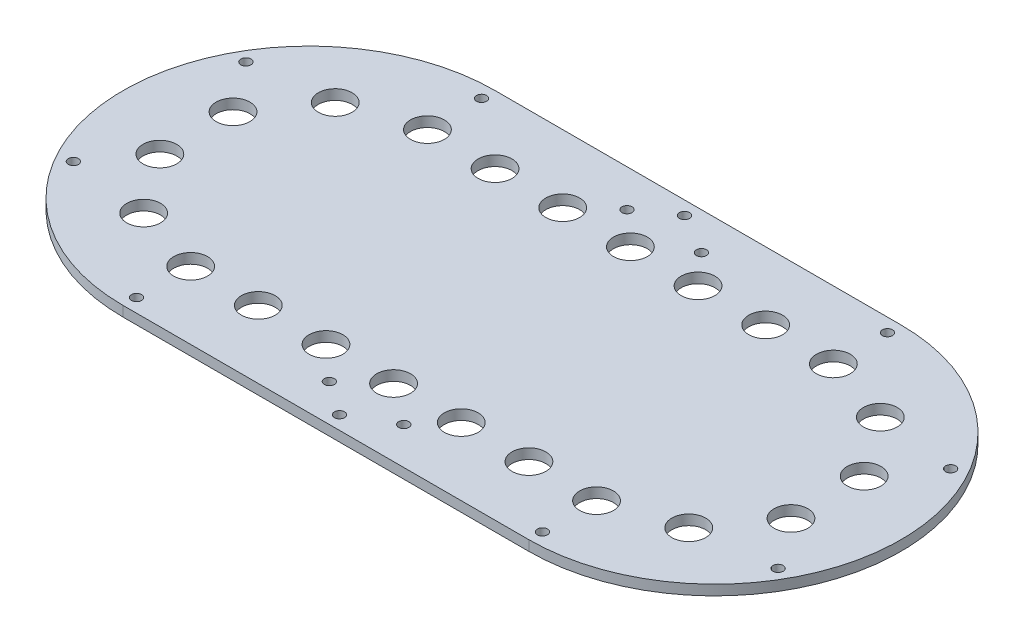
SolidWorks part; units mm, degrees
ref_plane "前视基准面" through (0, 0, 0) normal (0, 0, 1) x (1, 0, 0)
ref_plane "上视基准面" through (0, 0, 0) normal (0, 1, 0) x (1, 0, 0)
ref_plane "右视基准面" through (0, 0, 0) normal (1, 0, 0) x (0, 0, -1)
sketch "草图1" plane through (0, 0, 0) normal (0, 1, 0) x (1, 0, 0)
  line L0 (0, 0) -> (0, 89.0672) construction
  line L1 (-60, 0) -> (60, 0) construction
  line L2 (-60, 70) -> (60, 70)
  line L3 (-60, -70) -> (60, -70)
  line L4 (-90, 51.9615) -> (-60, 0) construction
  line L5 (-90, -51.9615) -> (-60, 0) construction
  line L8 (0, 0) -> (76.6344, 0) construction
  line L9 (-49.5811, 59.0885) -> (-60, 0) construction
  line L10 (-116.3816, -20.5212) -> (-60, 0) construction
  line L11 (-14.0373, -38.5673) -> (-60, 0) construction
  arc A2 (-60, 70) -> (-60, -70) centre (-60, 0) ccw
  arc A3 (60, -70) -> (60, 70) centre (60, 0) ccw
  circle A4 centre (0, 0) radius 1.5 construction
  circle A5 centre (-90, 51.9615) radius 1.5 construction
  circle A6 centre (-90, -51.9615) radius 1.5 construction
  circle A7 centre (90, -51.9615) radius 1.5 construction
  circle A8 centre (90, 51.9615) radius 1.5 construction
  circle A10 centre (-122, 0) radius 1.5
  circle A11 centre (122, 0) radius 1.5
  circle A12 centre (-30, 60) radius 1.5
  circle A13 centre (30, 60) radius 1.5
  circle A14 centre (30, -60) radius 1.5
  circle A15 centre (-30, -60) radius 1.5
  point P7 (0, 0)
  dimension "D4" = 3
  dimension "D7" = 3
  dimension "D9" = 3
  dimension "D10" = 60
  dimension "D12" = 3
  dimension "D13" = 62
  dimension "D14" = 62
  dimension "D15" = 3
  dimension "D16" = 3
  dimension "D18" = 60
  dimension "D8" = 120
  dimension "D11" = 120
  dimension "D17" = 30
  dimension "D20" = 60
  dimension "D21" = 80
  dimension "D24" = 120
  dimension "D26" = 60
  dimension "D27" = 120
extrude "凸台-拉伸2" add sketch "草图1" along normal blind 3
sketch "草图3" plane through (0, 3, 0) normal (0, 1, 0) x (1, 0, 0)
  line L2 (-60, -55) -> (60, -55)
  line L3 (60, 55) -> (-60, 55)
  line L4 (-60, -70) -> (60, -70)
  line L5 (60, 70) -> (-60, 70)
  line L6 (-60, -70) -> (60, -70)
  line L7 (60, 70) -> (-60, 70)
  arc A2 (60, -55) -> (60, 55) centre (60, 0) ccw
  arc A3 (-60, 55) -> (-60, -55) centre (-60, 0) ccw
  arc A4 (60, -70) -> (60, 70) centre (60, 0) ccw
  arc A5 (-60, 70) -> (-60, -70) centre (-60, 0) ccw
  arc A6 (60, -70) -> (60, 70) centre (60, 0) ccw
  arc A7 (-60, 70) -> (-60, -70) centre (-60, 0) ccw
  dimension "D1" = 0
  dimension "D2" = 15
extrude "切除-拉伸1" cut sketch "草图3" against normal blind 10
sketch "草图4" plane through (0, 3, 0) normal (0, 1, 0) x (1, 0, 0)
  line L2 (60, 35) -> (-60, 35) construction
  line L3 (-60, -35) -> (60, -35) construction
  line L6 (60, 55) -> (-60, 55)
  line L7 (-60, -55) -> (60, -55)
  line L8 (60, 55) -> (-60, 55) construction
  line L9 (-60, -55) -> (60, -55) construction
  line L10 (-1.65, 0) -> (1.65, 0) construction
  line L11 (0, -1.65) -> (0, 1.65) construction
  arc A2 (-60, 35) -> (-60, -35) centre (-60, 0) ccw construction
  arc A3 (60, -35) -> (60, 35) centre (60, 0) ccw construction
  arc A22 (-60, 55) -> (-60, -55) centre (-60, 0) ccw
  arc A23 (60, -55) -> (60, 55) centre (60, 0) ccw
  arc A24 (-60, 55) -> (-60, -55) centre (-60, 0) ccw construction
  arc A25 (60, -55) -> (60, 55) centre (60, 0) ccw construction
  circle A26 centre (-60, 35) radius 5
  circle A31 centre (-60, -35) radius 5
  circle A32 centre (-80.5725, -28.3156) radius 5
  circle A33 centre (-93.287, -10.8156) radius 5
  circle A34 centre (-93.287, 10.8156) radius 5
  circle A35 centre (-80.5725, 28.3156) radius 5
  circle A36 centre (-39.4275, 28.3156) radius 5 [skipped]
  circle A37 centre (-26.713, 10.8156) radius 5 [skipped]
  circle A38 centre (-26.713, -10.8156) radius 5 [skipped]
  circle A39 centre (-39.4275, -28.3156) radius 5 [skipped]
  circle A40 centre (-40, 35) radius 5
  circle A41 centre (-20, 35) radius 5
  circle A42 centre (0, 35) radius 5
  circle A43 centre (20, 35) radius 5
  circle A44 centre (40, 35) radius 5
  circle A45 centre (60, 35) radius 5
  circle A46 centre (60, -35) radius 5
  circle A47 centre (40, -35) radius 5
  circle A48 centre (20, -35) radius 5
  circle A49 centre (0, -35) radius 5
  circle A50 centre (-20, -35) radius 5
  circle A51 centre (-40, -35) radius 5
  circle A52 centre (80.5725, 28.3156) radius 5
  circle A53 centre (93.287, 10.8156) radius 5
  circle A54 centre (93.287, -10.8156) radius 5
  circle A55 centre (80.5725, -28.3156) radius 5
  point P34 (-60, 0)
  dimension "D3" = 10
  dimension "D4" = 10
  dimension "D5" = 7
  dimension "D2" = 20
  dimension "D1" = 0
extrude "切除-拉伸2" cut sketch "草图4" against normal blind 10
sketch "草图5" plane through (0, 3, 0) normal (0, 1, 0) x (1, 0, 0)
  line L0 (-60, -47) -> (60, -47) construction
  line L1 (60, 47) -> (-60, 47) construction
  line L2 (60, 55) -> (-60, 55)
  line L3 (-60, -55) -> (60, -55)
  line L5 (-60, -55) -> (60, -55) construction
  line L6 (60, 55) -> (-60, 55) construction
  line L7 (-1.65, 0) -> (1.65, 0) construction
  line L8 (0, -1.65) -> (0, 1.65) construction
  arc A0 (-60, 47) -> (-60, -47) centre (-60, 0) ccw construction
  arc A1 (60, -47) -> (60, 47) centre (60, 0) ccw construction
  arc A2 (-60, 55) -> (-60, -55) centre (-60, 0) ccw
  arc A3 (60, -55) -> (60, 55) centre (60, 0) ccw
  arc A4 (-60, 55) -> (-60, -55) centre (-60, 0) ccw construction
  arc A5 (60, -55) -> (60, 55) centre (60, 0) ccw construction
  circle A6 centre (-60, 51) radius 1.5
  circle A7 centre (0, 51) radius 1.5
  circle A8 centre (60, 51) radius 1.5
  circle A11 centre (-60, -51) radius 1.5
  circle A12 centre (-104.1673, -25.5) radius 1.5
  circle A13 centre (-104.1673, 25.5) radius 1.5
  circle A14 centre (-15.8327, -25.5) radius 1.5 [skipped]
  circle A15 centre (-15.8327, 25.5) radius 1.5 [skipped]
  circle A16 centre (60, -51) radius 1.5
  circle A17 centre (0, -51) radius 1.5
  circle A18 centre (-60, -51) radius 1.5
  circle A19 centre (104.1673, -25.5) radius 1.5
  circle A20 centre (104.1673, 25.5) radius 1.5
  point P30 (-60, 0)
  dimension "D3" = 3
  dimension "D4" = 4
  dimension "D1" = 0
  dimension "D2" = 8
  dimension "D5" = 3
  dimension "D6" = 6
extrude "切除-拉伸3" cut sketch "草图5" against normal blind 10 contours A8 | A20 | A19 | A16 | A17 | A11 | A12 | A13 | A6 | A7
sketch "草图6" plane through (0, 3, 0) normal (0, 1, 0) x (1, 0, 0)
  line L0 (-60, -47) -> (60, -47) construction
  line L3 (0, 0) -> (8.2148, 0) construction
  circle A0 centre (-10, -44) radius 1.5
  circle A3 centre (-10, 44) radius 1.5
  circle A4 centre (12, -44) radius 1.5
  circle A5 centre (12, 44) radius 1.5
  dimension "D1" = 3
  dimension "D2" = 3
  dimension "D3" = 10
  dimension "D4" = 3
  dimension "D5" = 12
  dimension "D6" = 3
extrude "切除-拉伸4" cut sketch "草图6" against normal blind 10
